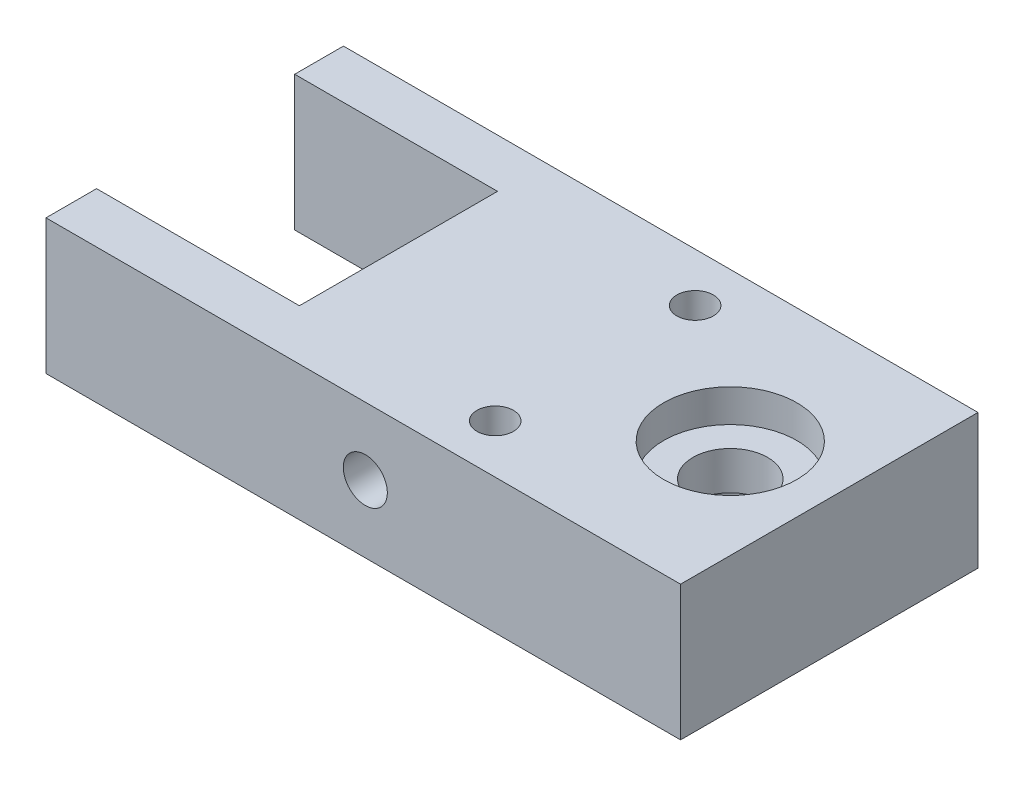
SolidWorks part; units mm, degrees
material "1060 Alloy"
ref_plane "Front Plane" through (0, 0, 0) normal (0, 0, 1) x (1, 0, 0)
ref_plane "Top Plane" through (0, 0, 0) normal (0, 1, 0) x (1, 0, 0)
ref_plane "Right Plane" through (0, 0, 0) normal (1, 0, 0) x (0, 0, -1)
sketch "Sketch1" plane through (0, 0, 0) normal (0, 1, 0) x (1, 0, 0)
  line L0 (0, 0) -> (-31.72, 0) construction
  line L1 (0, 0) -> (0, 18.4405) construction
  line L2 (-31.72, 9.53) -> (-31.72, -9.36)
  line L3 (-31.72, -9.36) -> (-51.06, -9.36)
  line L4 (-51.06, -9.36) -> (-51.06, -14.18)
  line L5 (-51.06, -14.18) -> (9.44, -14.18)
  line L6 (9.44, -14.18) -> (9.44, 14.18)
  line L7 (9.44, 14.18) -> (-51.06, 14.18)
  line L8 (-51.06, 14.18) -> (-51.06, 9.53)
  line L9 (-51.06, 9.53) -> (-31.72, 9.53)
  line L10 (-31.72, -9.46) -> (-31.72, 9) construction
  circle A0 centre (0, 0) radius 3.56
  circle A1 centre (0, 0) radius 8.474 construction
  dimension "D1" = 7.12
  dimension "D2" = 60.5
  dimension "D3" = 28.36
  dimension "D4" = 4.82
  dimension "D5" = 41.16
  dimension "D6" = 4.65
extrude "Boss-Extrude1" add sketch "Sketch1" along normal blind 12.86
sketch "Sketch2" plane through (-31.72, 0, 0) normal (-1, 0, 0) x (0, 0, 1)
  line L0 (-0.085, 6.43) -> (-0.085, 0) construction
  line L1 (-9.53, 0) -> (9.36, 0) construction
  line L2 (-0.085, 6.43) -> (-9.53, 6.43) construction
  line L3 (-9.53, 12.86) -> (-9.53, 0) construction
  circle A0 centre (-0.085, 6.43) radius 2.085
  dimension "D1" = 4.17
extrude "Cut-Extrude1" cut sketch "Sketch2" against normal blind 12.7
sketch "Sketch3" plane through (0, 12.86, 0) normal (0, 1, 0) x (-1, 0, 0)
  circle A0 centre (0, 0) radius 6.35
  dimension "D1" = 12.7
extrude "Cut-Extrude2" cut sketch "Sketch3" against normal blind 3.12
sketch "Sketch4" plane through (0, 0, 0) normal (0, -1, 0) x (1, 0, 0)
  circle A0 centre (0, 0) radius 5.57
  dimension "D1" = 11.14
extrude "Cut-Extrude3" cut sketch "Sketch4" against normal blind 6.08
sketch "Sketch5" plane through (0, 0, 0) normal (0, -1, 0) x (1, 0, 0)
  line L0 (-12.88, 9.53) -> (-12.88, -9.53) construction
  line L1 (0, 0) -> (-12.3777, 0) construction
  line L2 (-12.88, 7.79) -> (-4.8481, 7.79) construction
  line L3 (-12.88, -7.79) -> (-4.8481, -7.79) construction
  line L4 (-11.14, 9.53) -> (-11.14, -9.53) construction
  line L5 (9.44, 14.18) -> (9.44, -14.18) construction
  circle A0 centre (-12.88, -9.53) radius 1.74
  circle A1 centre (-12.88, 9.53) radius 1.74
  dimension "D2" = 3.48
  dimension "D1" = 15.58
  dimension "D3" = 20.58
extrude "Cut-Extrude4" cut sketch "Sketch5" against normal through all
sketch "Sketch6" plane through (0, 0, 14.18) normal (0, 0, 1) x (1, 0, 0)
  line L0 (9.44, 6.43) -> (-20.615, 6.43) construction
  line L1 (9.44, 12.86) -> (9.44, 0) construction
  line L2 (-18.88, 6.43) -> (-18.88, 0) construction
  line L3 (-51.06, 0) -> (9.44, 0) construction
  circle A0 centre (-20.615, 6.43) radius 1.735
  dimension "D2" = 3.47
  dimension "D1" = 28.32
extrude "8-32" cut sketch "Sketch6" against normal blind 5
sketch "Sketch7" plane through (0, 0, 14.18) normal (0, 0, 1) x (1, 0, 0)
  circle A0 centre (-20.615, 6.43) radius 2.1
  dimension "D1" = 4.2
extrude "Cut-Extrude5" cut sketch "Sketch7" against normal blind 10
cosmetic thread "Cosmetic Thread1" parameters "D1"=8, "D2"=5
